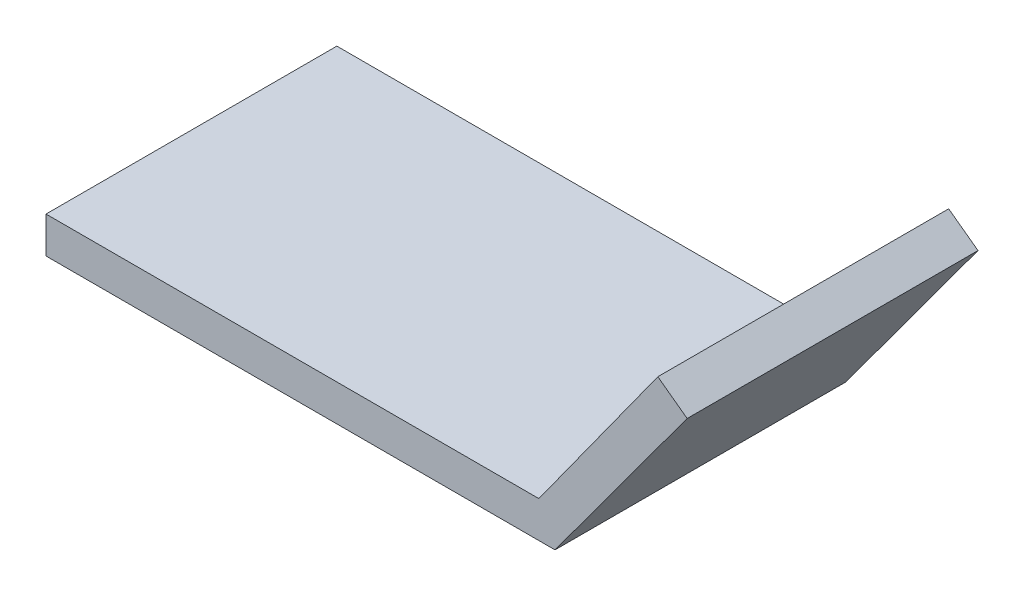
SolidWorks part; units mm, degrees
ref_plane "Front Plane" through (0, 0, 0) normal (0, 0, 1) x (1, 0, 0)
ref_plane "Top Plane" through (0, 0, 0) normal (0, 1, 0) x (1, 0, 0)
ref_plane "Right Plane" through (0, 0, 0) normal (1, 0, 0) x (0, 0, -1)
sketch "Sketch1" plane through (0, 0, 0) normal (0, 0, 1) x (1, 0, 0)
  line L0 (0, 0) -> (-44.45, 0)
  line L2 (-44.45, 0) -> (-44.45, 3.175)
  line L3 (-44.45, 3.175) -> (-1.408, 3.175)
  line L4 (-1.408, 3.175) -> (8.9808, 17.5874)
  line L5 (8.9808, 17.5874) -> (11.5395, 15.7076)
  line L6 (11.5395, 15.7076) -> (0, 0)
  dimension "D1" = 3.175
  dimension "D2" = 3.175
  dimension "D3" = 44.45
  dimension "D4" = 17.7664
  dimension "D5" = 19.4908
other "AlignGroup1"
other "AlignGroup2"
extrude "Boss-Extrude1" add sketch "Sketch1" along normal blind 25.4
